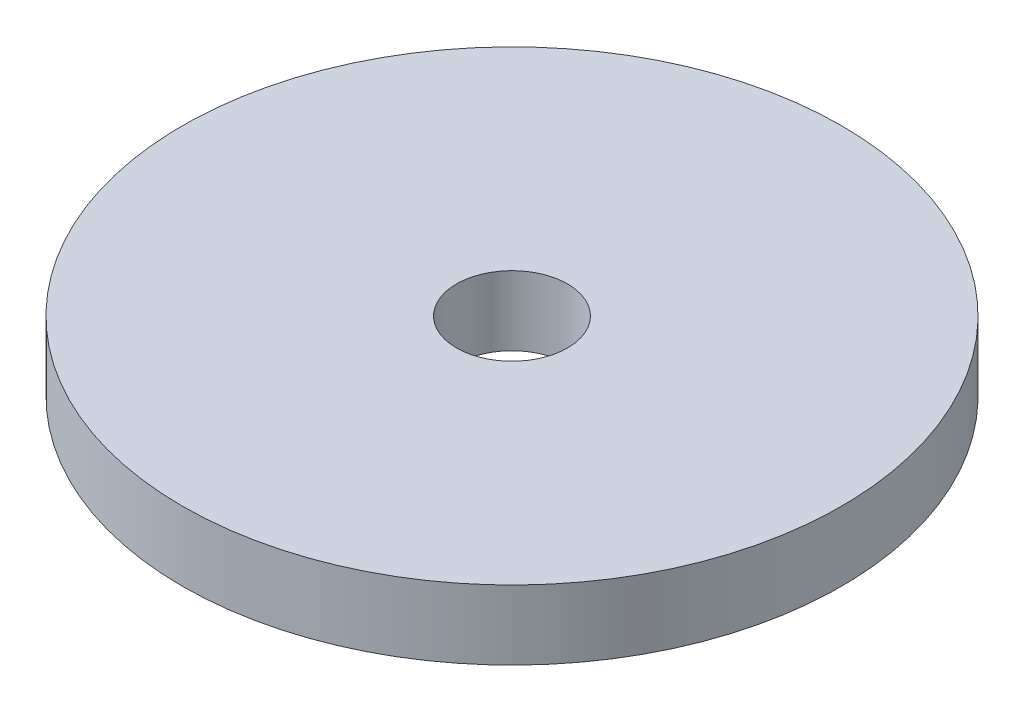
SolidWorks part; units mm, degrees
ref_plane "Front Plane" through (0, 0, 0) normal (0, 0, 1) x (1, 0, 0)
ref_plane "Top Plane" through (0, 0, 0) normal (0, 1, 0) x (1, 0, 0)
ref_plane "Right Plane" through (0, 0, 0) normal (1, 0, 0) x (0, 0, -1)
sketch "Sketch1" plane through (0, 0, 0) normal (0, 1, 0) x (1, 0, 0)
  circle A0 centre (0, 0) radius 12.065
  circle A1 centre (0, 0) radius 2.032
  dimension "D1" = 24.13
  dimension "D2" = 4.064
extrude "Boss-Extrude1" add sketch "Sketch1" along normal blind 2.54
